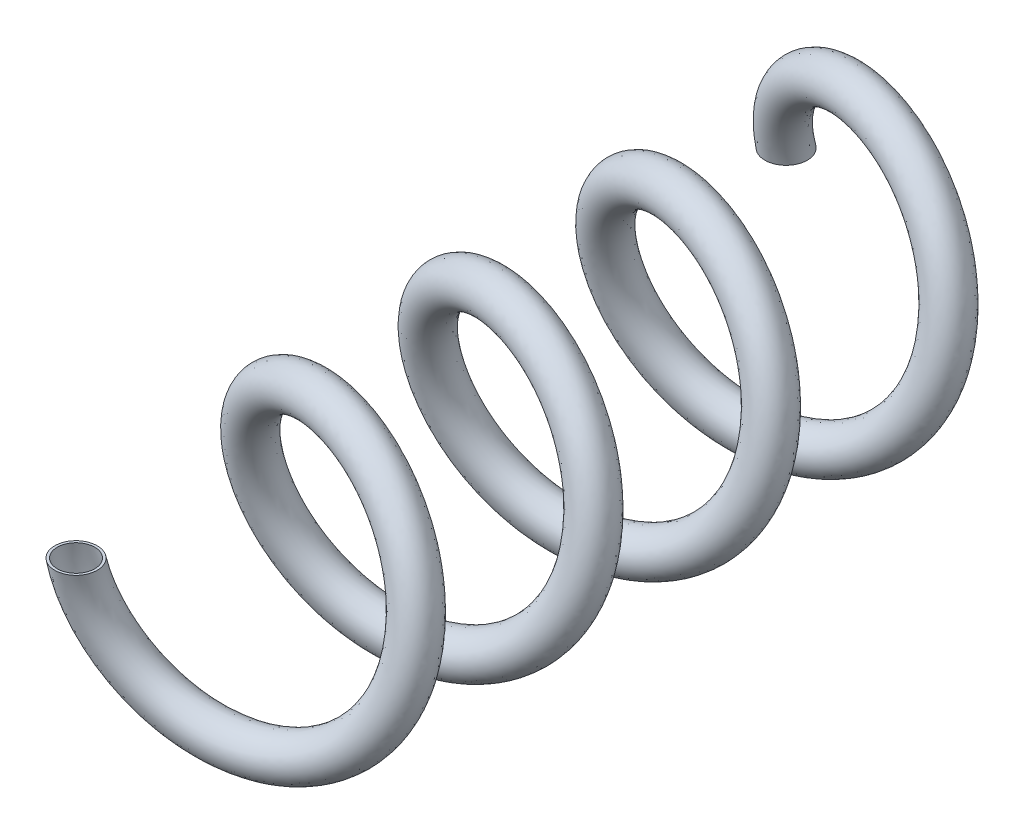
SolidWorks part; units mm, degrees
ref_plane "Front Plane" through (0, 0, 0) normal (0, 0, 1) x (1, 0, 0)
ref_plane "Top Plane" through (0, 0, 0) normal (0, 1, 0) x (1, 0, 0)
ref_plane "Right Plane" through (0, 0, 0) normal (1, 0, 0) x (0, 0, -1)
sketch "Sketch1" plane through (0, 0, 0) normal (0, 0, 1) x (1, 0, 0)
  circle A0 centre (0, 0) radius 35.4614
curve "Helix/Spiral1" pitch 50.8 height 203.2 turns 4
sketch "Sketch3" plane through (0, 0, 0) normal (0, 1, 0) x (1, 0, 0)
  circle A0 centre (-35.4614, 0) radius 6.0774
  circle A1 centre (-35.4614, 0) radius 5.3691
  spline S0 degree 3 poles (-35.4614, 0) (-35.4614, -0.6376) (-34.7938, -1.9176) (-31.8455, -3.8338) (-27.1153, -5.751) (-20.8679, -7.6679) (-13.4528, -9.5849) (-5.285, -11.5019) (3.1785, -13.4189) (11.4641, -15.3358) (19.1083, -17.2528) (25.6833, -19.1698) (30.8212, -21.0868) (34.2346, -23.0038) (35.7323, -24.9208) (35.2307, -26.8377) (32.7578, -28.7547) (28.452, -30.6717) (22.5541, -32.5887) (15.3943, -34.5057) (7.373, -36.4226) (-1.0607, -38.3396) (-9.4352, -40.2566) (-17.2816, -42.1736) (-24.1612, -44.0906) (-29.6887, -46.0075) (-33.5551, -47.9245) (-35.544, -49.8415) (-35.544, -51.7585) (-33.5551, -53.6755) (-29.6887, -55.5925) (-24.1612, -57.5094) (-17.2816, -59.4264) (-9.4352, -61.3434) (-1.0607, -63.2604) (7.373, -65.1774) (15.3943, -67.0943) (22.5541, -69.0113) (28.452, -70.9283) (32.7578, -72.8453) (35.2307, -74.7623) (35.7323, -76.6792) (34.2346, -78.5962) (30.8212, -80.5132) (25.6833, -82.4302) (19.1083, -84.3472) (11.4641, -86.2642) (3.1785, -88.1811) (-5.285, -90.0981) (-13.4528, -92.0151) (-20.8679, -93.9321) (-27.1153, -95.8491) (-31.8455, -97.766) (-34.7938, -99.683) (-35.7952, -101.6) (-34.7938, -103.517) (-31.8455, -105.434) (-27.1153, -107.3509) (-20.8679, -109.2679) (-13.4528, -111.1849) (-5.285, -113.1019) (3.1785, -115.0189) (11.4641, -116.9358) (19.1083, -118.8528) (25.6833, -120.7698) (30.8212, -122.6868) (34.2346, -124.6038) (35.7323, -126.5208) (35.2307, -128.4377) (32.7578, -130.3547) (28.452, -132.2717) (22.5541, -134.1887) (15.3943, -136.1057) (7.373, -138.0226) (-1.0607, -139.9396) (-9.4352, -141.8566) (-17.2816, -143.7736) (-24.1612, -145.6906) (-29.6887, -147.6075) (-33.5551, -149.5245) (-35.544, -151.4415) (-35.544, -153.3585) (-33.5551, -155.2755) (-29.6887, -157.1925) (-24.1612, -159.1094) (-17.2816, -161.0264) (-9.4352, -162.9434) (-1.0607, -164.8604) (7.373, -166.7774) (15.3943, -168.6943) (22.5541, -170.6113) (28.452, -172.5283) (32.7578, -174.4453) (35.2307, -176.3623) (35.7323, -178.2792) (34.2346, -180.1962) (30.8212, -182.1132) (25.6833, -184.0302) (19.1083, -185.9472) (11.4641, -187.8642) (3.1785, -189.7811) (-5.285, -191.6981) (-13.4528, -193.6151) (-20.8679, -195.5321) (-27.1153, -197.449) (-31.8455, -199.3662) (-34.7938, -201.2824) (-35.4614, -202.5624) (-35.4614, -203.2) knots 0 0 0 0 0.009434 0.018868 0.028302 0.037736 0.04717 0.056604 0.066038 0.075472 0.084906 0.09434 0.103774 0.113208 0.122642 0.132075 0.141509 0.150943 0.160377 0.169811 0.179245 0.188679 0.198113 0.207547 0.216981 0.226415 0.235849 0.245283 0.254717 0.264151 0.273585 0.283019 0.292453 0.301887 0.311321 0.320755 0.330189 0.339623 0.349057 0.358491 0.367925 0.377358 0.386792 0.396226 0.40566 0.415094 0.424528 0.433962 0.443396 0.45283 0.462264 0.471698 0.481132 0.490566 0.5 0.509434 0.518868 0.528302 0.537736 0.54717 0.556604 0.566038 0.575472 0.584906 0.59434 0.603774 0.613208 0.622642 0.632075 0.641509 0.650943 0.660377 0.669811 0.679245 0.688679 0.698113 0.707547 0.716981 0.726415 0.735849 0.745283 0.754717 0.764151 0.773585 0.783019 0.792453 0.801887 0.811321 0.820755 0.830189 0.839623 0.849057 0.858491 0.867925 0.877358 0.886792 0.896226 0.90566 0.915094 0.924528 0.933962 0.943396 0.95283 0.962264 0.971698 0.981132 0.990566 1 1 1 1 construction
sweep "Sweep1" add profiles "Sketch3" path "Helix/Spiral1"
